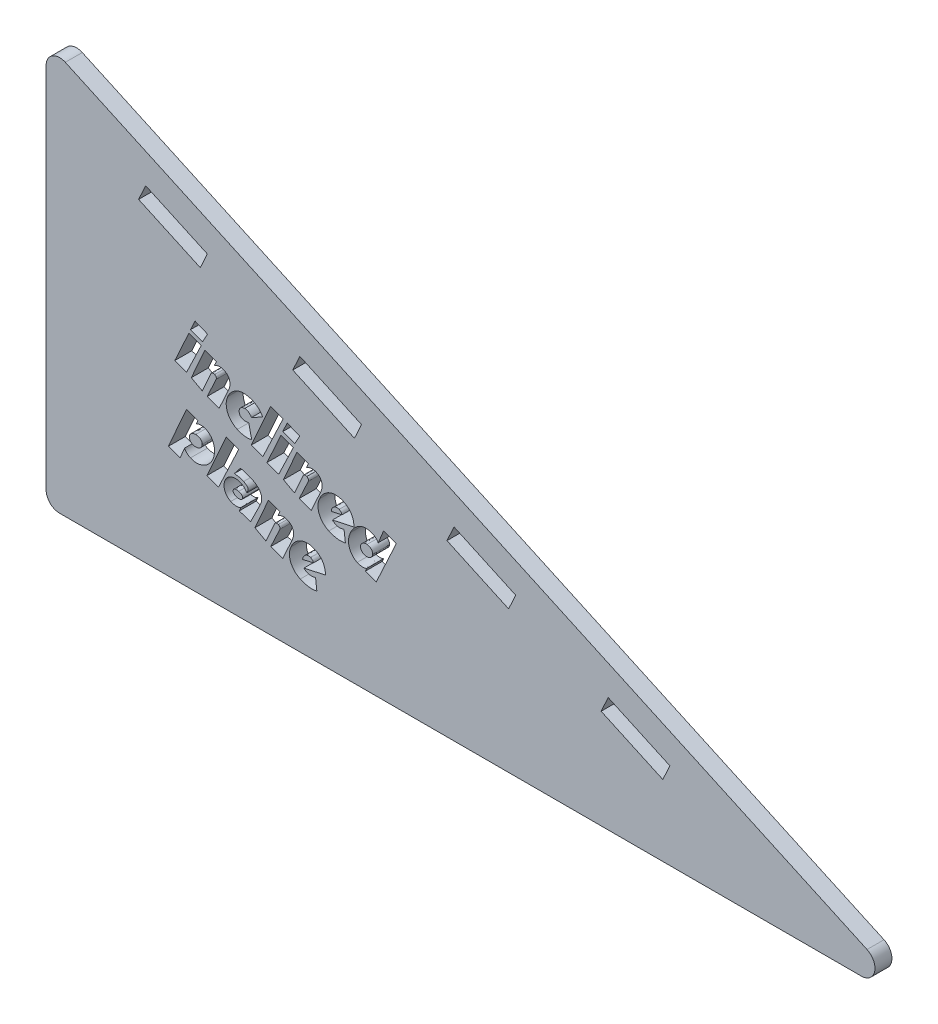
SolidWorks part; units mm, degrees
ref_plane "Front Plane" through (0, 0, 0) normal (0, 0, 1) x (1, 0, 0)
ref_plane "Top Plane" through (0, 0, 0) normal (0, 1, 0) x (1, 0, 0)
ref_plane "Right Plane" through (0, 0, 0) normal (1, 0, 0) x (0, 0, -1)
sketch "Sketch1" plane through (0, 0, 0) normal (0, 0, 1) x (1, 0, 0)
  line L0 (0, 71.3317) -> (0, 2.54)
  line L1 (2.54, 0) -> (152.6257, 0)
  line L2 (153.684, 4.849) -> (3.5983, 73.6407)
  arc A0 (0, 71.3317) -> (3.5983, 73.6407) centre (2.54, 71.3317) cw
  arc A1 (0, 2.54) -> (2.54, 0) centre (2.54, 2.54) ccw
  arc A2 (152.6257, 0) -> (153.684, 4.849) centre (152.6257, 2.54) ccw
  point P6 (0, 75.29)
  point P9 (0, 0)
  point P12 (164.2633, 0)
  dimension "D3" = 2.54
  dimension "D4" = 2.54
  dimension "D1" = 165.1
  dimension "D2" = 11.6376
  dimension "D5" = 68.7917
extrude "Extrude1" add sketch "Sketch1" along normal blind 3.175
sketch "Sketch2" plane through (0, 0, 3.175) normal (0, 0, 1) x (1, 0, 0)
  line L0 (0, 66.2092) -> (144.4513, 0) construction
  line L1 (0, 71.3317) -> (0, 2.54) construction
  line L2 (2.54, 0) -> (152.6257, 0) construction
  line L3 (153.684, 4.849) -> (3.5983, 73.6407) construction
  line L4 (17.3176, 58.2717) -> (18.6405, 61.1579)
  line L5 (0, 66.2092) -> (10.8471, 89.8747) construction
  line L6 (30.1856, 55.8663) -> (28.8626, 52.98)
  line L7 (28.8626, 52.98) -> (17.3176, 58.2717)
  line L8 (46.1802, 45.0425) -> (47.5031, 47.9288)
  line L9 (47.5031, 47.9288) -> (59.0482, 42.6371)
  line L10 (59.0482, 42.6371) -> (57.7253, 39.7508)
  line L11 (57.7253, 39.7508) -> (46.1802, 45.0425)
  line L12 (75.0428, 31.8133) -> (76.3658, 34.6996)
  line L14 (87.9108, 29.4079) -> (86.5879, 26.5217)
  line L15 (86.5879, 26.5217) -> (75.0428, 31.8133)
  line L16 (76.3658, 34.6996) -> (87.9108, 29.4079)
  line L17 (72.2257, 33.1046) -> (85.0659, 61.1187) construction
  line L18 (55.04, 38.886) -> (61.7226, 53.4657) construction
  line L19 (18.6405, 61.1579) -> (30.1856, 55.8663)
  line L20 (116.7735, 16.1788) -> (105.2284, 21.4704)
  line L21 (103.9055, 18.5842) -> (105.2284, 21.4704)
  line L23 (14.6323, 57.4069) -> (26.1774, 52.1152) [skipped]
  line L24 (55.04, 38.886) -> (60.8125, 36.2402) [skipped]
  line L25 (72.3576, 30.9485) -> (83.9026, 25.6569) [skipped]
  line L26 (103.9055, 18.5842) -> (115.4505, 13.2925)
  line L27 (115.4505, 13.2925) -> (116.7735, 16.1788)
  dimension "D1" = 3.175
  dimension "D2" = 12.7
  dimension "D3" = 19.05
  dimension "D4" = 158.902
  dimension "D5" = 19.05
  dimension "D6" = 3
  dimension "D7" = 19.05
  dimension "D8" = 5.08
  dimension "D9" = 19.05
extrude "Cut-Extrude1" cut sketch "Sketch2" against normal through all
sketch "Sketch5" plane through (0, 0, 3.175) normal (0, 0, 1) x (1, 0, 0)
  line L0 (0, 71.3317) -> (0, 2.54) construction
  line L1 (0, 46.7006) -> (101.8887, 0) construction
  line L2 (153.684, 4.849) -> (3.5983, 73.6407) construction
  line L3 (0, 33.7901) -> (73.7213, 0) construction
  line L5 (2.54, 0) -> (152.6257, 0) construction
  text T0 "        inclined" font "GROBOLD" height in points 36
  text T1 "plane" font "GROBOLD" height in points 36
extrude "Cut-Extrude3" cut sketch "Sketch5" against normal through all
